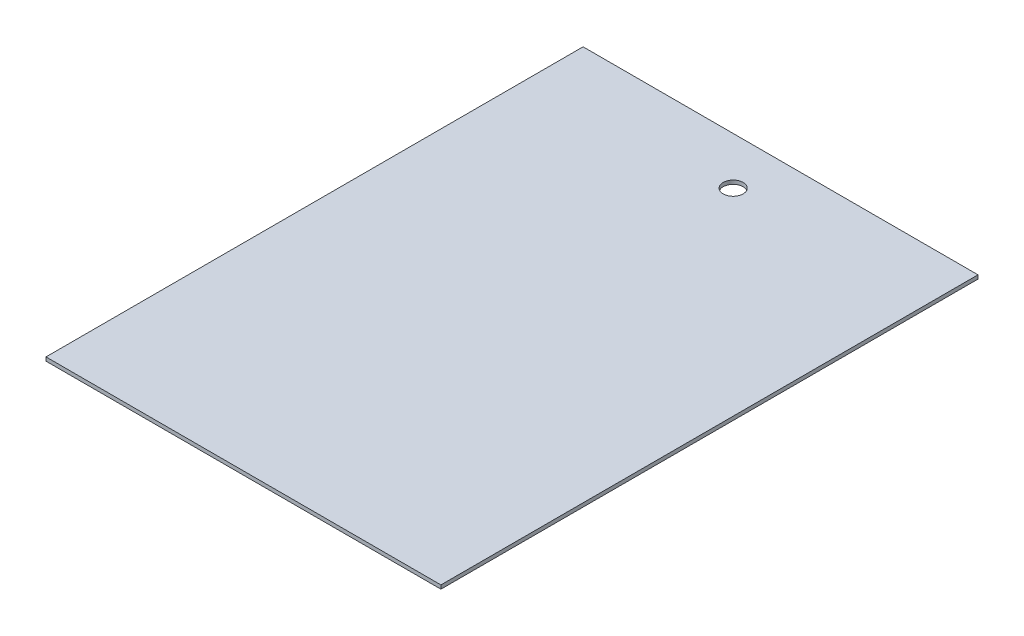
SolidWorks part; units mm, degrees
ref_plane "Front Plane" through (0, 0, 0) normal (0, 0, 1) x (1, 0, 0)
ref_plane "Top Plane" through (0, 0, 0) normal (0, 1, 0) x (1, 0, 0)
ref_plane "Right Plane" through (0, 0, 0) normal (1, 0, 0) x (0, 0, -1)
sketch "Sketch1" plane through (0, 0, 0) normal (0, 1, 0) x (1, 0, 0)
  line L1 (-158.75, 215.9) -> (158.75, 215.9)
  line L2 (-158.75, 215.9) -> (-158.75, -215.9)
  line L3 (-158.75, -215.9) -> (158.75, -215.9)
  line L4 (158.75, 215.9) -> (158.75, -215.9)
  line L5 (-158.75, 215.9) -> (158.75, -215.9) construction
  line L6 (-158.75, -215.9) -> (158.75, 215.9) construction
  point P0 (0, 0)
  dimension "D1" = 317.5
  dimension "D2" = 431.8
extrude "Boss-Extrude1" add sketch "Sketch1" along normal blind 3
sketch "Sketch2" plane through (0, 3, 0) normal (0, 1, 0) x (1, 0, 0)
  circle A0 centre (0, 177.8) radius 8
  dimension "D1" = 16
  dimension "D2" = 177.8
extrude "Cut-Extrude1" cut sketch "Sketch2" against normal through all
